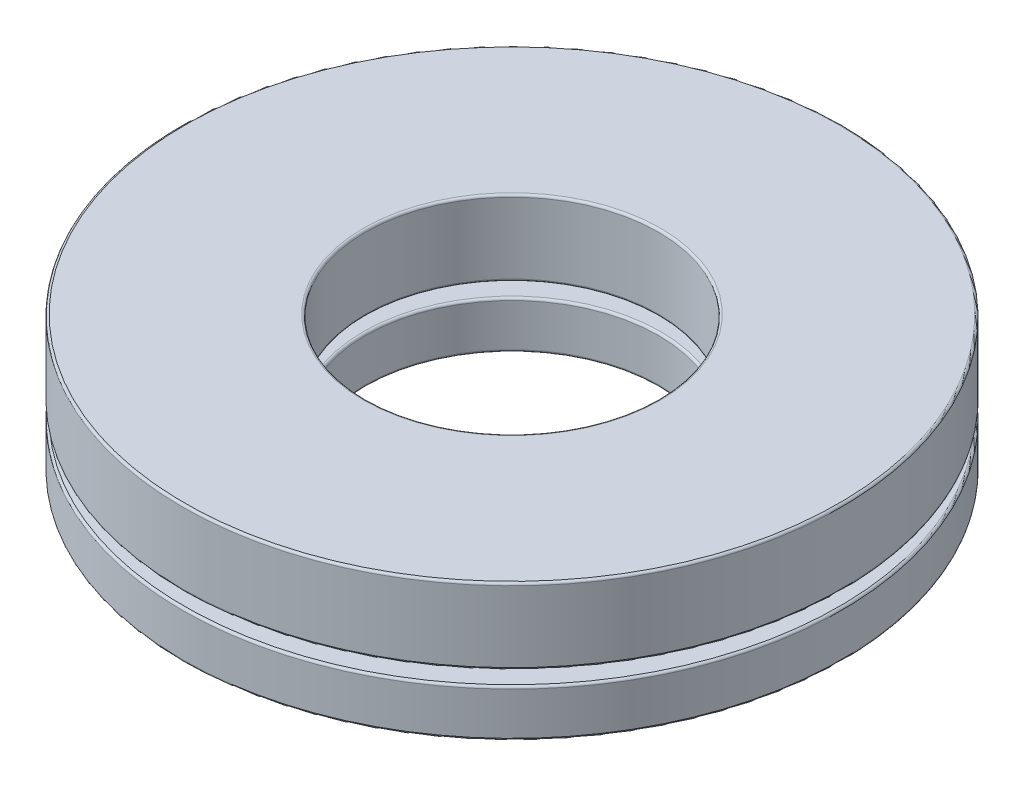
SolidWorks part; units mm, degrees
ref_plane "Front Plane" through (0, 0, 0) normal (0, 0, 1) x (1, 0, 0)
ref_plane "Top Plane" through (0, 0, 0) normal (0, 1, 0) x (1, 0, 0)
ref_plane "Right Plane" through (0, 0, 0) normal (1, 0, 0) x (0, 0, -1)
sketch "Sketch1" plane through (0, 0, 0) normal (1, 0, 0) x (0, 0, -1)
  line L0 (-7.1438, 0) -> (7.1438, 0) construction
  line L1 (0, -2.4511) -> (0, 2.4511) construction
  line L2 (-7.1438, 0.5106) -> (-3.175, 0.5106)
  line L3 (-7.1438, 0.5106) -> (-7.1438, -0.5106)
  line L4 (-7.1438, -0.5106) -> (-3.175, -0.5106)
  line L5 (-3.175, 0.5106) -> (-3.175, -0.5106)
  line L6 (-5.1594, 0.817) -> (-5.1594, -0.817) construction
  circle A0 centre (-5.1594, 0) radius 0.817 construction
  point P13 (-5.1594, 0.5106)
  dimension "OD" = 14.2875
  dimension "Shaft Dia" = 6.35
  dimension "Th" = 4.9022
  dimension "D1" = 1.6341
  dimension "D2" = 1.0213
revolve "Revolve1" add sketch "Sketch1" angle 360 about L1
sketch "Sketch3" plane through (0, 0, 0) normal (1, 0, 0) x (0, 0, -1)
  line L0 (-5.1594, 0.817) -> (-5.1594, -0.817)
  arc A0 (-5.1594, 0.817) -> (-5.1594, -0.817) centre (-5.1594, 0) ccw
  circle A1 centre (-5.1594, 0) radius 0.817 construction
revolve "Cut-Revolve1" cut sketch "Sketch3" angle 360 about L0
sketch "Sketch2" plane through (0, 0, 0) normal (1, 0, 0) x (0, 0, -1)
  line L0 (-5.1594, 0.817) -> (-5.1594, -0.817)
  arc A0 (-5.1594, 0.817) -> (-5.1594, -0.817) centre (-5.1594, 0) ccw
  circle A2 centre (-5.1594, 0) radius 0.817 construction
revolve "Revolve2" add sketch "Sketch2" angle 360 about L0
ref_axis "Axis1" through (0, 2.4511, 0) along (0, -1, 0)
pattern_circular "CirPattern1" count 7 every 51.429 about axis through (0, 2.4511, 0) along (0, -1, 0) of bodies 187
pattern_circular "CirPattern2" count 7 every 51.429 about axis through (0, 0, 0) along (0, 1, 0) of "Cut-Revolve1"
sketch "Sketch4" plane through (0, 0, 0) normal (1, 0, 0) x (0, 0, -1)
  line L0 (-7.1438, 0.5106) -> (-7.1438, -0.5106) construction
  line L1 (-7.1438, 0.817) -> (-3.175, 0.817)
  line L2 (-7.1438, 0.817) -> (-7.1438, 2.4511)
  line L3 (-7.1438, 2.4511) -> (-3.175, 2.4511)
  line L4 (-3.175, 0.817) -> (-3.175, 2.4511)
  line L10 (-3.175, 0.5106) -> (-3.175, -0.5106) construction
  line L11 (0, 0) -> (-7.1438, 0) construction
  line L12 (-7.1438, 0) -> (7.1438, 0) construction
  dimension "D1" = 1.6341
  dimension "D2" = 3.9688
revolve "Revolve3" add sketch "Sketch4" angle 360 about L1
fillet "Fillet1" radius 0.049 4 edges at (0, 0.817, -3.175) (0, 2.4511, -3.175) (0, 0.817, -7.1438) (0, 2.4511, -7.1438)
fillet "Fillet2" radius 0.049 4 edges at (0, -0.5106, -3.175) (0, 0.5106, -3.175) (0, -0.5106, -7.1438) (0, 0.5106, -7.1438)
equation "\"D1@Sketch1\" = \"Th@Sketch1\"/3"
equation "\"D2@Sketch1\" = \"D1@Sketch1\"*.625"
equation "\"Balls@CirPattern1\" = \"OD@Sketch1\"*12"
equation "\"Angle@CirPattern1\" = 360/\"Balls@CirPattern1\""
equation "\"D1@CirPattern2\" = \"Balls@CirPattern1\""
equation "\"D2@CirPattern2\" = \"Angle@CirPattern1\""
equation "\"D1@Fillet1\" = \"Th@Sketch1\"*.01"
equation "\"D1@Fillet2\" = \"D1@Fillet1\""
equation "\"D1@Fillet3\" = \"D1@Fillet1\""
